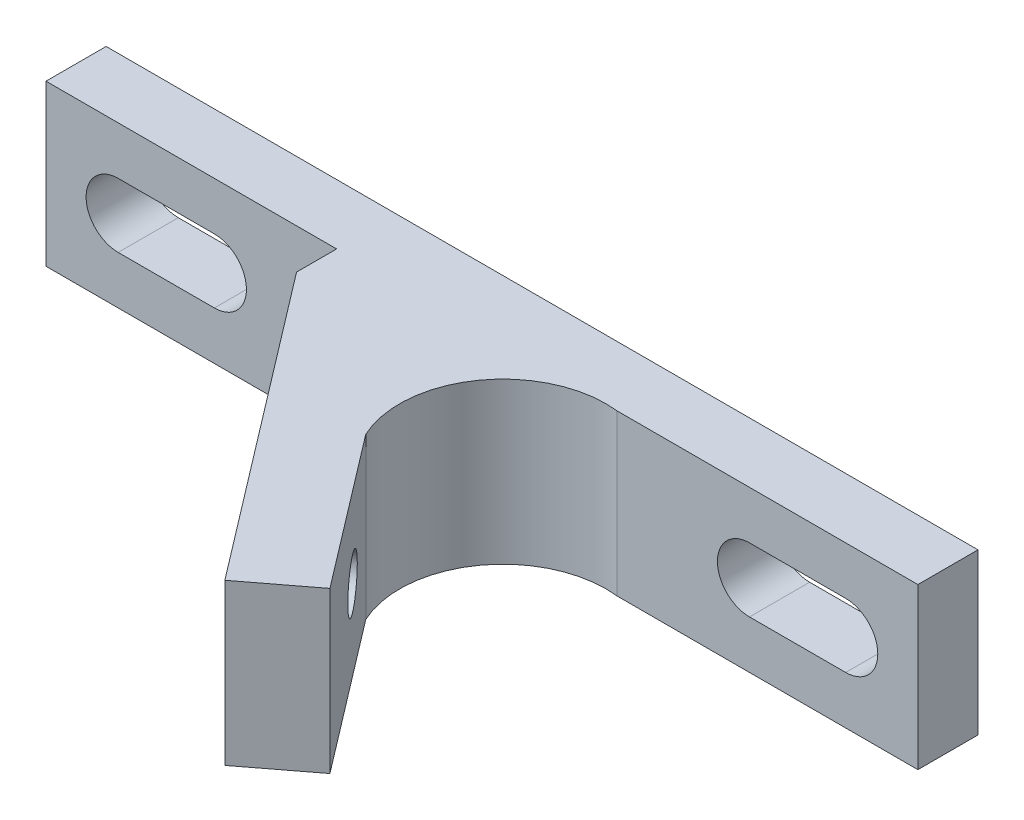
SolidWorks part; units mm, degrees
ref_plane "Спереди" through (0, 0, 0) normal (0, 0, 1) x (1, 0, 0)
ref_plane "Сверху" through (0, 0, 0) normal (0, 1, 0) x (1, 0, 0)
ref_plane "Справа" through (0, 0, 0) normal (1, 0, 0) x (0, 0, -1)
sketch "Эскиз1" plane through (0, 0, 0) normal (0, 1, 0) x (1, 0, 0)
  line L0 (-21.75, 0) -> (21.75, 0)
  line L1 (-21.75, 0) -> (-21.75, -3)
  line L2 (21.75, 0) -> (21.75, -3)
  line L3 (21.75, -3) -> (6.75, -3)
  line L4 (-21.75, -3) -> (-7.25, -3)
  line L5 (-7.25, -3) -> (-7.25, -5)
  line L6 (-7.25, -5) -> (4.2768, -20.1041)
  line L7 (4.2768, -20.1041) -> (7.25, -17.8351)
  line L8 (7.25, -17.8351) -> (1.4866, -10.283)
  arc A0 (1.4866, -10.283) -> (6.75, -3) centre (6.1597, -8.1168) cw
  dimension "D13" = 5.1507
  dimension "D1" = 43.5
  dimension "D2" = 21.75
  dimension "D3" = 90
  dimension "D4" = 3
  dimension "D5" = 14.5
  dimension "D6" = 2
  dimension "D7" = 3
  dimension "D8" = 15
  dimension "D9" = 19
  dimension "D10" = 3.7401
  dimension "D11" = 14.5
  dimension "D12" = 9.5
extrude "Бобышка-Вытянуть1" add sketch "Эскиз1" along normal blind 8
sketch "Эскиз2" plane through (0, 0, 0) normal (0, 0, -1) x (-1, 0, 0)
  line L0 (-18.15, 4) -> (-13.35, 4) construction
  line L1 (-18.15, 5.6) -> (-13.35, 5.6)
  line L2 (-18.15, 2.4) -> (-13.35, 2.4)
  line L3 (0, 16.818) -> (0, -18.0136) construction
  line L4 (18.15, 4) -> (13.35, 4) construction
  line L5 (18.15, 5.6) -> (13.35, 5.6)
  line L6 (18.15, 2.4) -> (13.35, 2.4)
  arc A0 (-18.15, 5.6) -> (-18.15, 2.4) centre (-18.15, 4) ccw
  arc A1 (-13.35, 2.4) -> (-13.35, 5.6) centre (-13.35, 4) ccw
  arc A2 (18.15, 5.6) -> (18.15, 2.4) centre (18.15, 4) cw
  arc A3 (13.35, 2.4) -> (13.35, 5.6) centre (13.35, 4) cw
  point P2 (-15.75, 4)
  point P13 (15.75, 4)
  dimension "D1" = 4
  dimension "D2" = 1.6
  dimension "D3" = 3.6
  dimension "D4" = 4.8
extrude "Вырез-Вытянуть1" cut sketch "Эскиз2" against normal up to next
sketch "Эскиз3" plane through (-6.993, 0, 5.3368) normal (-0.795, 0, 0.6067) x (0.6067, 0, 0.795)
  circle A0 centre (12.5764, 4) radius 1.25
  circle A1 centre (3.0764, 4) radius 1.25
  point P7 (3.4584, -4.086)
  dimension "D1" = 2.5
  dimension "D4" = 2.5
  dimension "D2" = 6
  dimension "D3" = 4
  dimension "D5" = 4
  dimension "D6" = 9.5
extrude "Вырез-Вытянуть2" cut sketch "Эскиз3" against normal blind 6
